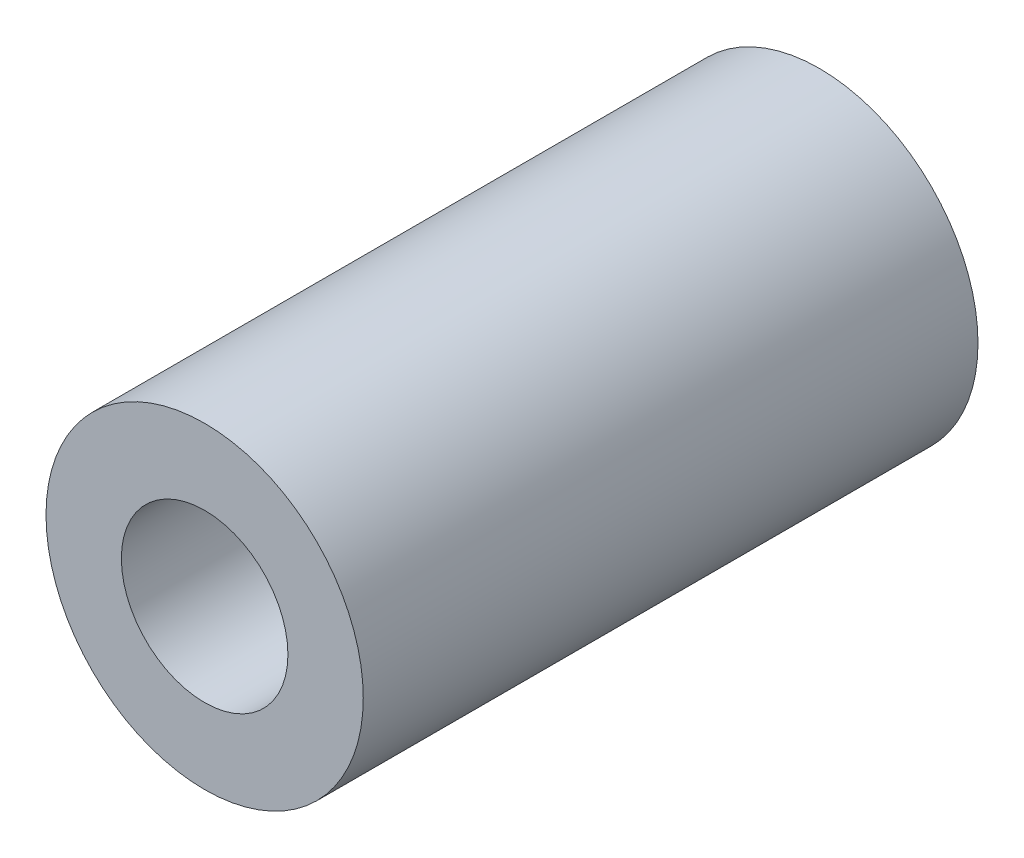
SolidWorks part; units mm, degrees
ref_plane "正面" through (0, 0, 0) normal (0, 0, 1) x (1, 0, 0)
ref_plane "平面" through (0, 0, 0) normal (0, 1, 0) x (1, 0, 0)
ref_plane "右側面" through (0, 0, 0) normal (1, 0, 0) x (0, 0, -1)
sketch "ｽｹｯﾁ1" plane through (0, 0, 0) normal (0, 0, 1) x (1, 0, 0)
  circle A0 centre (0, 0) radius 2.1
  circle A1 centre (0, 0) radius 4
  dimension "D1" = 4.2
  dimension "D2" = 8
extrude "ﾎﾞｽ - 押し出し1" add sketch "ｽｹｯﾁ1" along normal blind 15.5
